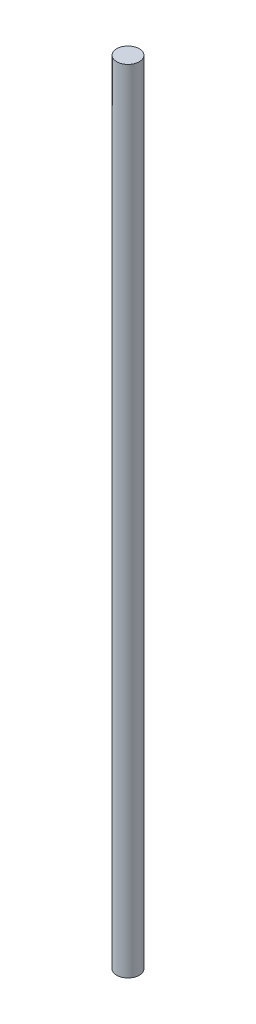
SolidWorks part; units mm, degrees
ref_plane "Plano frontal" through (0, 0, 0) normal (0, 0, 1) x (1, 0, 0)
ref_plane "Plano superior" through (0, 0, 0) normal (0, 1, 0) x (1, 0, 0)
ref_plane "Plano direito" through (0, 0, 0) normal (1, 0, 0) x (0, 0, -1)
sketch "Esboço1" plane through (0, 0, 0) normal (0, 1, 0) x (1, 0, 0)
  circle A0 centre (0, 0) radius 4
  dimension "D1" = 8
extrude "Ressalto-extrusão1" add sketch "Esboço1" along normal mid plane 280.5
